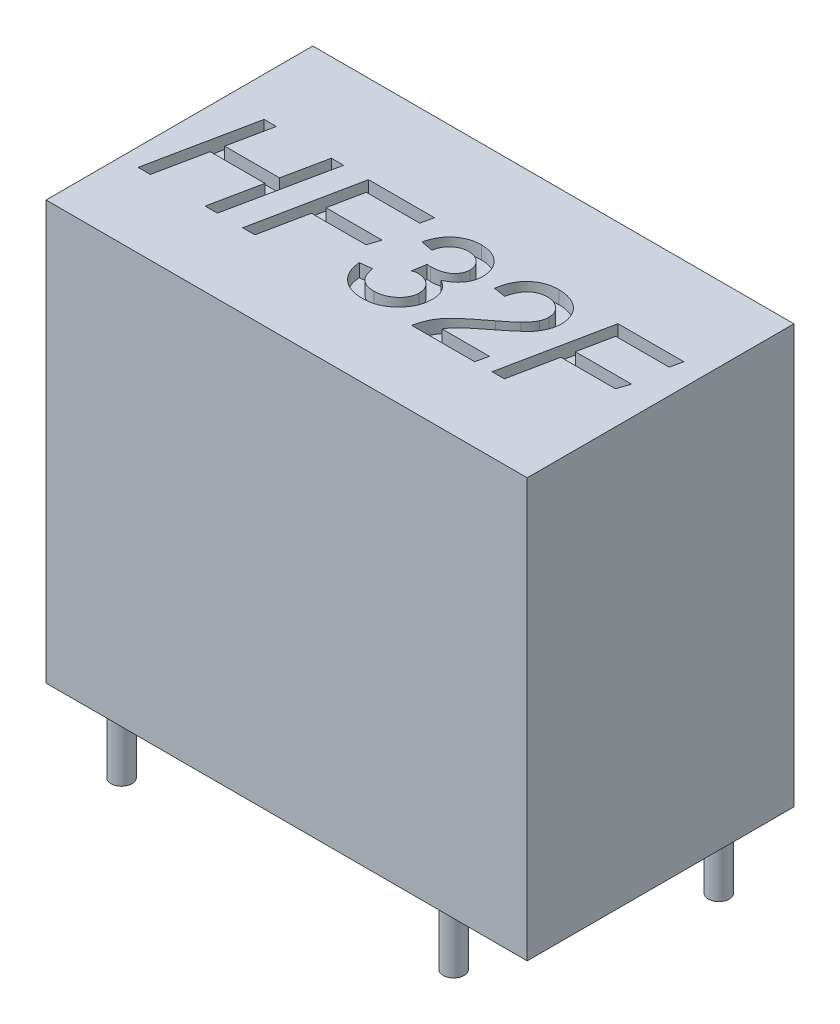
SolidWorks part; units mm, degrees
ref_plane "Спереди" through (0, 0, 0) normal (0, 0, 1) x (1, 0, 0)
ref_plane "Сверху" through (0, 0, 0) normal (0, 1, 0) x (1, 0, 0)
ref_plane "Справа" through (0, 0, 0) normal (1, 0, 0) x (0, 0, -1)
sketch "Эскиз1" plane through (0, 0, 0) normal (0, 1, 0) x (1, 0, 0)
  line L1 (-9.1974, 5.0908) -> (9.2026, 5.0908)
  line L2 (-9.1974, 5.0908) -> (-9.1974, -5.1092)
  line L3 (-9.1974, -5.1092) -> (9.2026, -5.1092)
  line L4 (9.2026, 5.0908) -> (9.2026, -5.1092)
  line L5 (-9.1974, 5.0908) -> (9.2026, -5.1092) construction
  line L6 (-9.1974, -5.1092) -> (9.2026, 5.0908) construction
  point P0 (0.0026, -0.0092)
  point P5 (0.0026, -0.0092)
  dimension "D1" = 10.2
  dimension "D2" = 18.4
extrude "Бобышка-Вытянуть1" add sketch "Эскиз1" along normal blind 16
sketch "Эскиз2" plane through (0, 16, 0) normal (0, 1, 0) x (1, 0, 0)
  text T0 "HF32F"
  point P1 (-9.1168, -2.5067)
  point P2 (-10.6751, -2.5277)
  point P3 (-11.8754, -2.6541)
  point P4 (-7.6934, -2.7567)
  point P5 (-8.7752, -2.8378)
  point P6 (-8.7752, -2.2698)
extrude "Вырез-Вытянуть1" cut sketch "Эскиз2" against normal blind 0.5
sketch "Эскиз3" plane through (0, 0, 0) normal (0, -1, 0) x (1, 0, 0)
  circle A0 centre (-7.62, 3.8) radius 0.4
  circle A1 centre (-7.62, -3.8) radius 0.4
  circle A2 centre (5.08, 3.8) radius 0.4
  circle A3 centre (7.62, -3.8) radius 0.4
  dimension "D1" = 0.8
  dimension "D2" = 0.8
  dimension "D3" = 0.8
  dimension "D4" = 0.8
  dimension "D6" = 7.6
  dimension "D7" = 3.8
  dimension "D8" = 7.6
  dimension "D9" = 12.7
  dimension "D10" = 2.54
  dimension "D11" = 7.62
  dimension "D12" = 7.62
  dimension "D5" = 3.8
extrude "Бобышка-Вытянуть2" add sketch "Эскиз3" along normal blind 3
